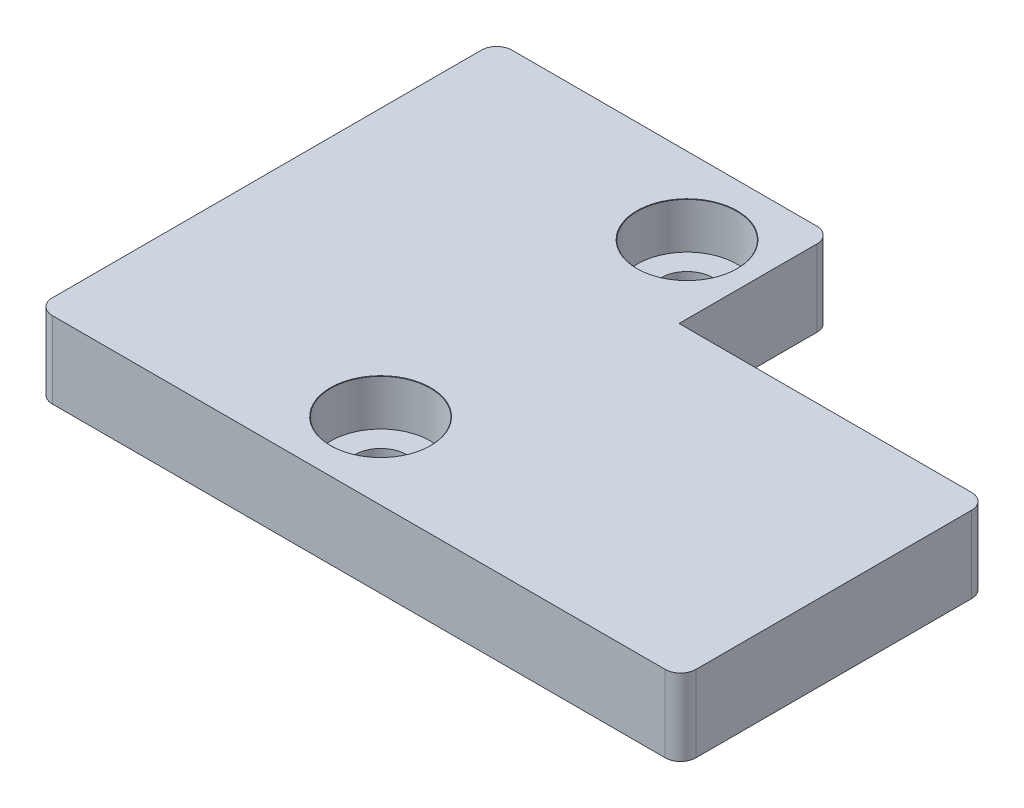
SolidWorks part; units mm, degrees
ref_plane "Front Plane" through (0, 0, 0) normal (0, 0, 1) x (1, 0, 0)
ref_plane "Top Plane" through (0, 0, 0) normal (0, 1, 0) x (1, 0, 0)
ref_plane "Right Plane" through (0, 0, 0) normal (1, 0, 0) x (0, 0, -1)
sketch "Sketch1" plane through (0, 0, 0) normal (0, 1, 0) x (1, 0, 0)
  line L1 (21, 10) -> (-21, 10)
  line L2 (21, 10) -> (21, -10)
  line L3 (21, -10) -> (-21, -10)
  line L4 (-21, 10) -> (-21, -10)
  line L5 (21, 10) -> (-21, -10) construction
  line L6 (21, -10) -> (-21, 10) construction
  point P0 (0, 0)
  dimension "D1" = 42
  dimension "D2" = 20
extrude "Boss-Extrude1" add sketch "Sketch1" along normal blind 5
sketch "Sketch2" plane through (0, 5, 0) normal (0, 1, 0) x (1, 0, 0)
  line L0 (21, -10) -> (21, 10) construction
  line L1 (-21, 10) -> (0.9, 10)
  line L2 (-21, 10) -> (-21, 20)
  line L3 (-21, 20) -> (0.9, 20)
  line L4 (0.9, 10) -> (0.9, 20)
  dimension "D1" = 20.1
  dimension "D2" = 10
extrude "Boss-Extrude2" add sketch "Sketch2" against normal blind 5
sketch "Sketch3" plane through (0, 5, 0) normal (0, 1, 0) x (1, 0, 0)
  line L0 (-21, 5) -> (21, 5) construction
  line L1 (-21, 20) -> (-21, -10) construction
  line L2 (21, -10) -> (21, 10) construction
  line L3 (-3.575, 20) -> (-3.575, -10) construction
  line L4 (0.9, 20) -> (-21, 20) construction
  line L5 (-21, -10) -> (21, -10) construction
  line L6 (0.9, 10) -> (0.9, 20) construction
  line L7 (-3.575, 15) -> (-3.575, -5) construction
  point P17 (-3.575, 5)
  dimension "D1" = 4.475
  dimension "D2" = 20
hole_wizard "CBORE for M3 SHCS1" positions "Sketch6" profile "Sketch7" counterbore size "M3" standard "ANSI Metric" end condition through all
sketch "Sketch6" plane through (0, 5, 0) normal (0, 1, 0) x (1, 0, 0)
  point P0 (-3.575, 15)
  point P3 (-3.575, -5)
sketch "Sketch7" plane through (-3.575, 5, -15) normal (1, 0, 0) x (0, 0, 1)
  line L0 (0, 0) -> (0, 5)
  line L1 (0, 5) -> (1.7, 5)
  line L3 (1.7, 5) -> (1.7, 3)
  line L4 (3.25, 3) -> (1.7, 3)
  line L5 (3.25, 3) -> (3.25, 0.021)
  line L6 (3.25, 0.021) -> (3.275, 0)
  line L7 (3.275, 0) -> (0, 0)
  line L8 (-3.25, 0.021) -> (-3.275, 0) construction
  line L11 (0, -6.35) -> (0, 107.95) construction
  dimension "Thru Hole Dia." = 3.4
  dimension "Thru Hole Depth" = 5
  dimension "C'Bore Dia." = 6.5
  dimension "C'Bore Depth" = 3
  dimension "Near C'Sink Dia." = 6.55
  dimension "Near C'Sink Angle" = 100
fillet "Fillet1" radius 1 5 edges at (-21, 2.5, -20) (0.9, 2.5, -20) (21, 2.5, -10) (21, 2.5, 10) (-21, 2.5, 10)
